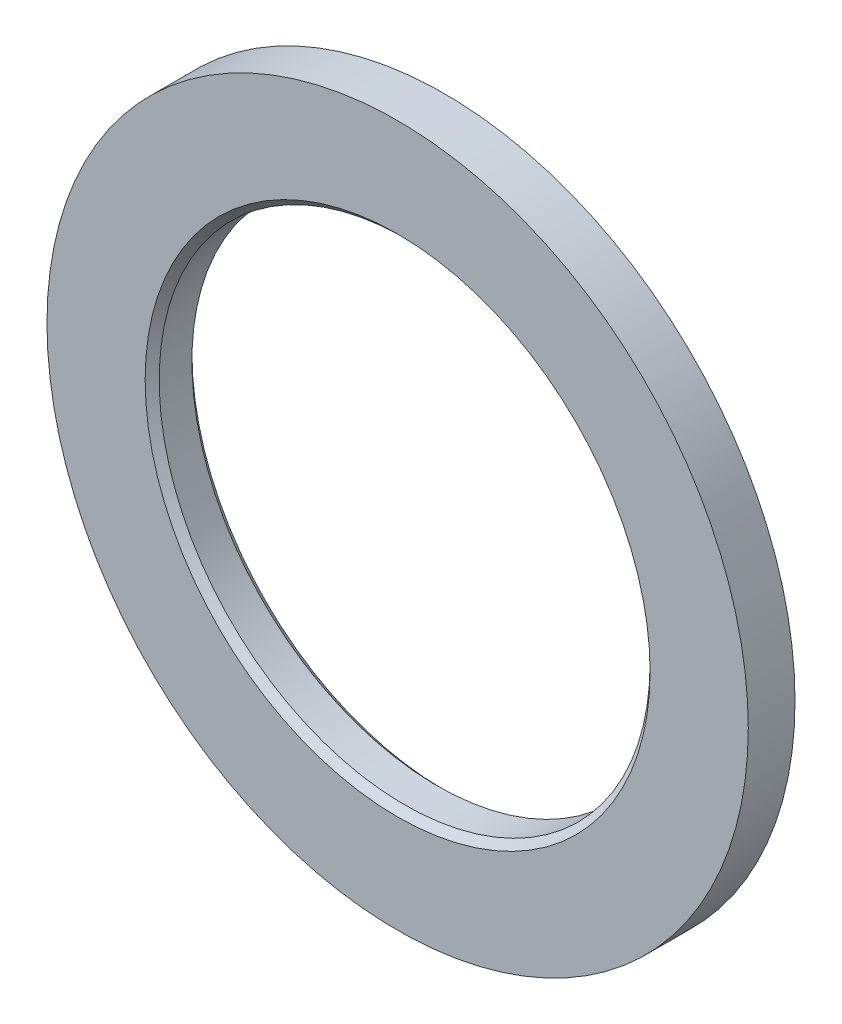
SolidWorks part; units mm, degrees
ref_plane "Front" through (0, 0, 0) normal (0, 0, 1) x (1, 0, 0)
ref_plane "Top" through (0, 0, 0) normal (0, 1, 0) x (1, 0, 0)
ref_plane "Right" through (0, 0, 0) normal (1, 0, 0) x (0, 0, -1)
sketch "Guard base" plane through (0, 0, 0) normal (0, 0, 1) x (1, 0, 0)
  circle A0 centre (0, 0) radius 37.5
  dimension "D1" = 75
extrude "Guard" add sketch "Guard base" along normal blind 5
sketch "Axle hole base" plane through (0, 0, 5) normal (0, 0, 1) x (1, 0, 0)
  circle A0 centre (0, 0) radius 26.25
  dimension "D1" = 52.5
extrude "Axle hole" cut sketch "Axle hole base" against normal through all
ref_axis "Center Z" through (0, 0, 0) along (0, 0, -1)
sketch "Mate ring room base" plane through (0, 0, 0) normal (0, 1, 0) x (1, 0, 0)
  line L0 (26.25, -5) -> (27, -5)
  line L1 (27, -5) -> (26.25, -4.25)
  line L2 (26.25, -4.25) -> (26.25, -5)
  line L5 (26.25, 0) -> (27, 0)
  line L6 (26.25, 0) -> (26.25, -0.75)
  line L7 (26.25, -0.75) -> (27, 0)
  dimension "D1" = 0.75
revolve "Mate ring room" cut sketch "Mate ring room base" angle 360 about axis through (0, 0, 0) along (0, 0, -1)
equation "\"mate_room\"= 0.25"
equation "\"removal_room\"= 0.75"
equation "\"large_inner_axle_diameter\"=20"
equation "\"D1@Axle hole base\"  = \"53_71_spool_inner_diameter\" - \"spool_inner_diameter_room\" + \"mate_room\" * 2"
equation "\"guard_thickness\"=5"
equation "\"spool_inner_diameter_room\"=1"
equation "\"D1@Guard\"=\"guard_thickness\""
equation "\"32_92_guard_diameter\"=50"
equation "\"D1@Guard base\" = \"53_71_guard_diameter\""
equation "\"32_92_spool_inner_diameter\"=32"
equation "\"32_92_spool_thickness\"=92"
equation "\"D1@Mate ring room base\" = \"removal_room\""
equation "\"bend_room_length_multiplier\"=3"
equation "\"small_inner_axle_diameter\"=17"
equation "\"32_92_extra_spool_thickness\"=-5"
equation "\"39_92_spool_inner_diameter\"=39"
equation "\"39_92_spool_thickness\"=92"
equation "\"39_92_guard_diameter\"=60"
equation "\"53_55_spool_inner_diameter\"=53"
equation "\"53_55_spool_thickness\"=55"
equation "\"53_55_guard_diameter\"=75"
equation "\"52_62_spool_inner_diameter\"=52"
equation "\"52_62_spool_thickness\"=62"
equation "\"52_62_guard_diameter\"=75"
equation "\"53_71_spool_inner_diameter\"=53"
equation "\"53_71_spool_thickness\"=71"
equation "\"53_71_guard_diameter\"=75"
